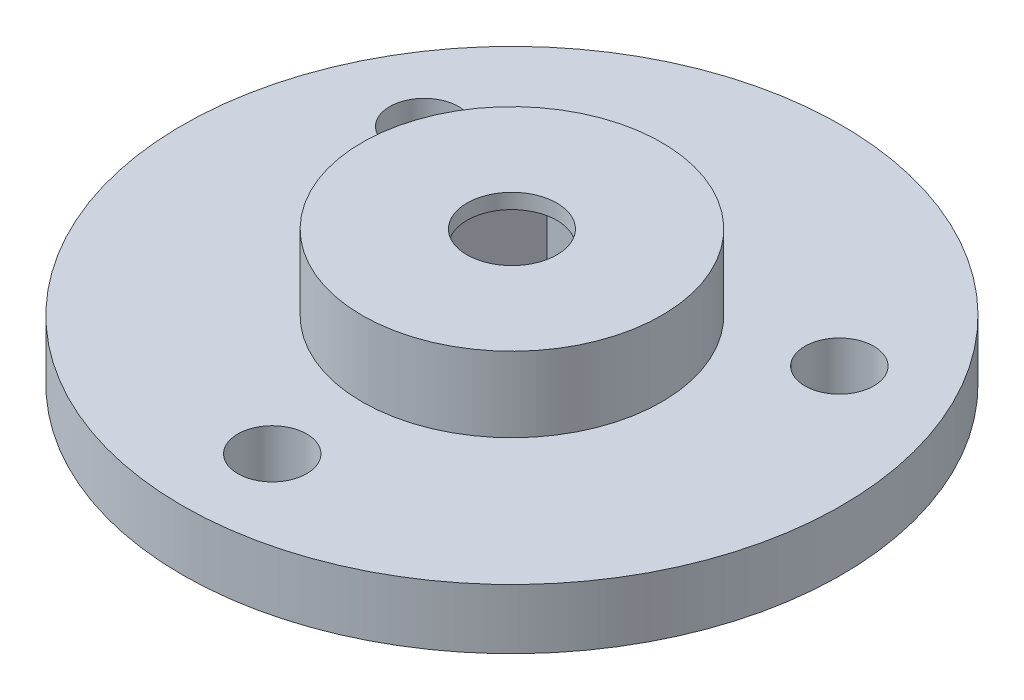
SolidWorks part; units mm, degrees
ref_plane "Ön Düzlem" through (0, 0, 0) normal (0, 0, 1) x (1, 0, 0)
ref_plane "Üst Düzlem" through (0, 0, 0) normal (0, 1, 0) x (1, 0, 0)
ref_plane "Sağ Düzlem" through (0, 0, 0) normal (1, 0, 0) x (0, 0, -1)
sketch "Sketch1" plane through (0, 0, 0) normal (0, 1, 0) x (1, 0, 0)
  line L1 (3.1754, 0) -> (1.5877, 2.75)
  line L2 (1.5877, 2.75) -> (-1.5877, 2.75)
  line L3 (-1.5877, 2.75) -> (-3.1754, 0)
  line L4 (-3.1754, 0) -> (-1.5877, -2.75)
  line L5 (-1.5877, -2.75) -> (1.5877, -2.75)
  line L6 (1.5877, -2.75) -> (3.1754, 0)
  circle A0 centre (0, 0) radius 11
  circle A1 centre (0, -8) radius 1.15
  circle A2 centre (-6.9282, 4) radius 1.15
  circle A3 centre (6.9282, 4) radius 1.15
  circle A4 centre (0, 0) radius 2.75 construction
  point P11 (0, 0)
  dimension "D1" = 22
  dimension "D2" = 2.3
  dimension "D4" = 8
  dimension "D5" = 5.5
  dimension "D3" = 3
extrude "Boss-Extrude1" add sketch "Sketch1" along normal blind 2
sketch "Sketch3" plane through (0, 2, 0) normal (0, 1, 0) x (1, 0, 0)
  line L0 (3.1754, 0) -> (1.5877, 2.75) construction
  line L1 (1.5877, -2.75) -> (3.1754, 0) construction
  line L2 (-1.5877, -2.75) -> (1.5877, -2.75) construction
  line L3 (-3.1754, 0) -> (-1.5877, -2.75) construction
  line L4 (-1.5877, 2.75) -> (-3.1754, 0) construction
  line L5 (1.5877, 2.75) -> (-1.5877, 2.75) construction
  line L6 (3.1754, 0) -> (1.5877, 2.75)
  line L7 (1.5877, -2.75) -> (3.1754, 0)
  line L8 (-1.5877, -2.75) -> (1.5877, -2.75)
  line L9 (-3.1754, 0) -> (-1.5877, -2.75)
  line L10 (-1.5877, 2.75) -> (-3.1754, 0)
  line L11 (1.5877, 2.75) -> (-1.5877, 2.75)
  circle A0 centre (0, 0) radius 5
  dimension "D1" = 10
extrude "Boss-Extrude3" add sketch "Sketch3" along normal mid plane 4
sketch "Sketch4" plane through (0, 4, 0) normal (0, 1, 0) x (1, 0, 0)
  circle A0 centre (0, 0) radius 5
  circle A1 centre (0, 0) radius 1.5
  circle A2 centre (0, 0) radius 5 construction
  dimension "D1" = 3
extrude "Boss-Extrude4" add sketch "Sketch4" along normal blind 0.5
